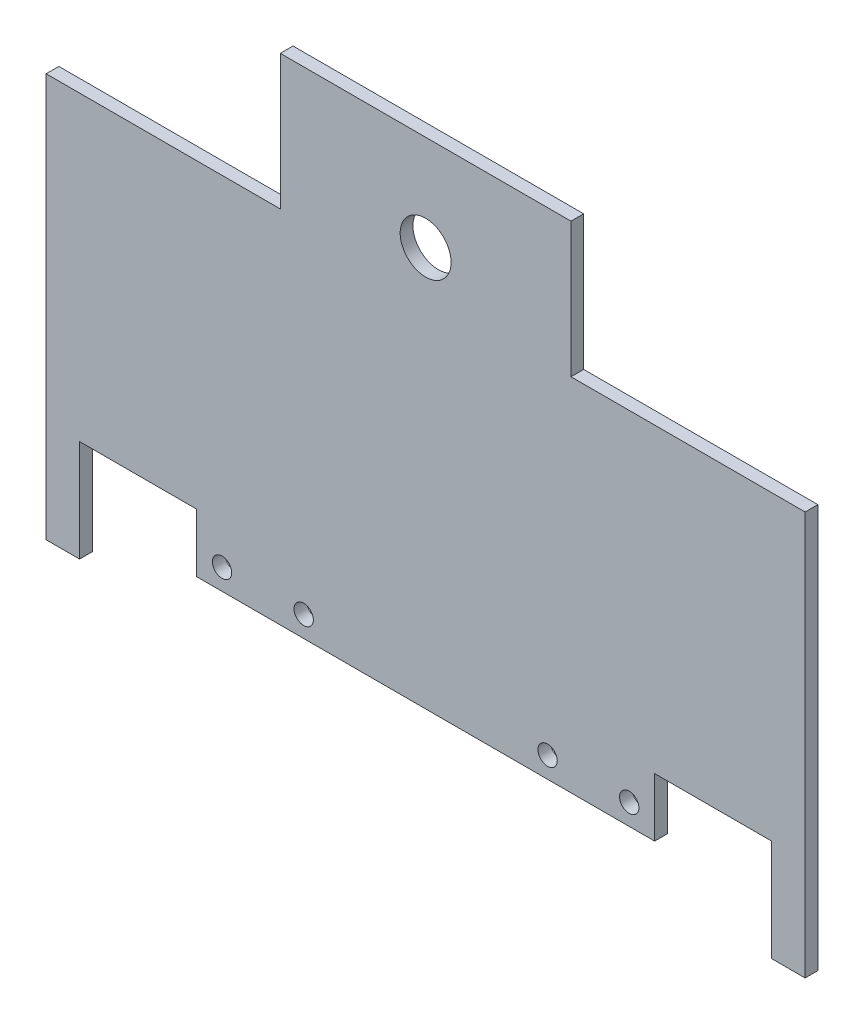
SolidWorks part; units mm, degrees
ref_plane "Front Plane" through (0, 0, 0) normal (0, 0, 1) x (1, 0, 0)
ref_plane "Top Plane" through (0, 0, 0) normal (0, 1, 0) x (1, 0, 0)
ref_plane "Right Plane" through (0, 0, 0) normal (1, 0, 0) x (0, 0, -1)
sketch "Sketch1" plane through (0, 0, 0) normal (0, 0, 1) x (1, 0, 0)
  line L0 (-55.6532, -29.7927) -> (-55.6532, -15.1902) construction
  line L1 (92.5946, -6.8779) -> (92.5946, 60.1262)
  line L2 (92.5946, 60.1262) -> (34.152, 60.1262)
  line L3 (-59.2607, -29.7927) -> (55.0393, -29.7927)
  line L4 (-96.8159, 60.1262) -> (-96.8159, -6.8779)
  line L5 (-59.2607, -15.1902) -> (-88.4707, -15.1902)
  line L6 (-88.4707, -15.1902) -> (-88.4707, -40.5902)
  line L7 (-88.4707, -40.5902) -> (-96.8159, -40.5902)
  line L8 (-2.1107, 31.2539) -> (-2.1107, 60.1262) construction
  line L9 (-96.8159, -6.8779) -> (-96.8159, -40.5902)
  line L10 (92.5946, -6.8779) -> (92.5946, -40.5902)
  line L11 (-59.2607, -15.1902) -> (-59.2607, -29.7927)
  line L12 (-2.1107, 31.2539) -> (-2.1107, -29.7927) construction
  line L13 (34.152, 60.1262) -> (34.152, 93.757)
  line L14 (55.0393, -15.1902) -> (84.2493, -15.1902)
  line L15 (48.6893, -29.7927) -> (48.6893, -24.5679) construction
  line L16 (48.6893, -24.5679) -> (55.0393, -24.5679) construction
  line L17 (84.2493, -40.5902) -> (92.5946, -40.5902)
  line L18 (84.2493, -15.1902) -> (84.2493, -40.5902)
  line L19 (55.0393, -15.1902) -> (55.0393, -29.7927)
  line L20 (48.6893, -24.5679) -> (28.322, -24.5679) construction
  line L21 (34.152, 93.757) -> (-38.3733, 93.757)
  line L22 (-38.3733, 60.1262) -> (-38.3733, 93.757)
  line L23 (-38.3733, 60.1262) -> (-96.8159, 60.1262)
  circle A0 centre (48.6893, -24.5679) radius 2.413
  circle A1 centre (28.322, -24.5679) radius 2.413
  circle A2 centre (-32.5433, -24.5679) radius 2.413
  circle A3 centre (-52.9107, -24.5679) radius 2.413
  circle A4 centre (-2.1107, 69.8925) radius 6.35
  dimension "D9" = 4.826
  dimension "D10" = 4.826
  dimension "D2" = 12.7
  dimension "D1" = 114.3
  dimension "D3" = 14.6025
  dimension "D4" = 29.21
  dimension "D5" = 25.4
  dimension "D6" = 14.6025
  dimension "D7" = 5.2248
  dimension "D8" = 6.35
extrude "Boss-Extrude1" add sketch "Sketch1" along normal blind 3.175
